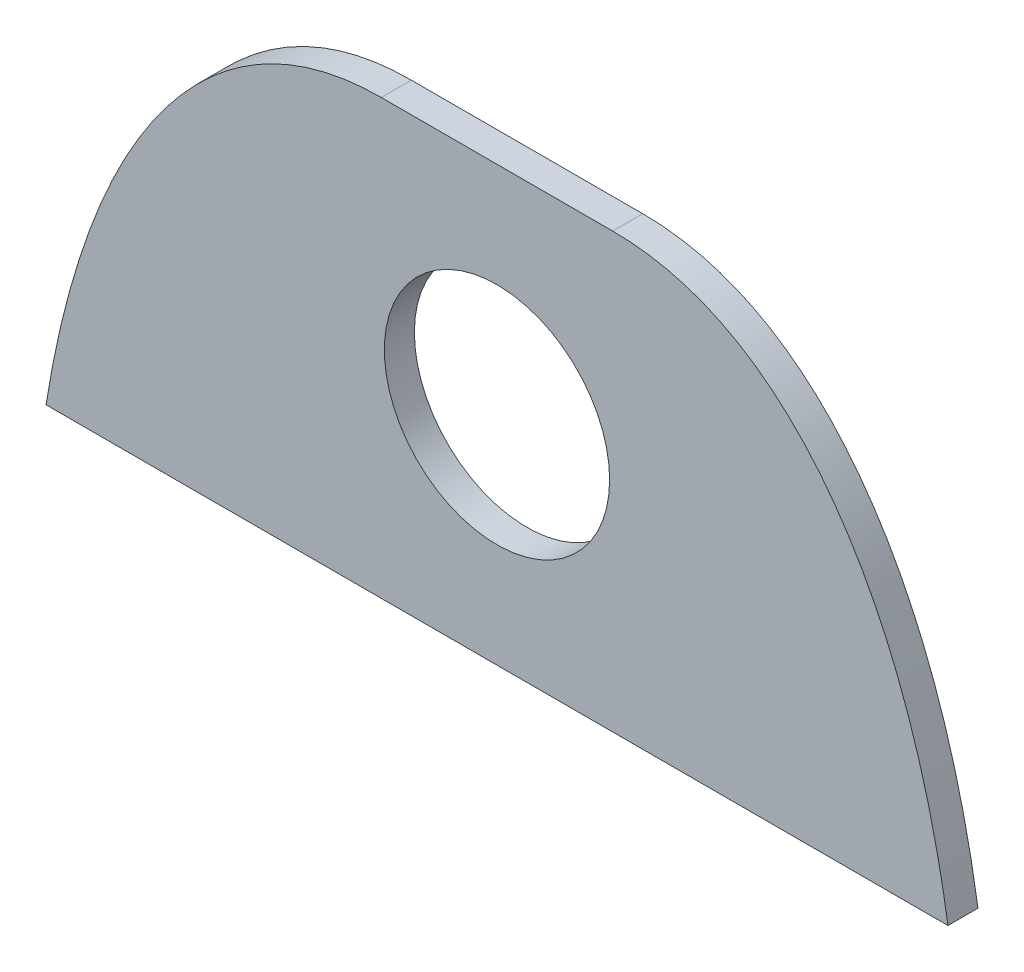
SolidWorks part; units mm, degrees
ref_plane "Front Plane" through (0, 0, 0) normal (0, 0, 1) x (1, 0, 0)
ref_plane "Top Plane" through (0, 0, 0) normal (0, 1, 0) x (1, 0, 0)
ref_plane "Right Plane" through (0, 0, 0) normal (1, 0, 0) x (0, 0, -1)
sketch "Sketch1" plane through (0, 0, 0) normal (0, 0, 1) x (1, 0, 0)
  line L0 (0, 0) -> (15.2522, 0)
  line L1 (9.5827, 7.3353) -> (5.6695, 7.3353)
  spline S0 degree 3 poles (5.6695, 7.3353) (5.244, 7.3353) (4.8287, 7.2747) (4.2224, 7.0847) (4.0246, 7.0051) (3.6475, 6.8192) (3.4665, 6.7125) (3.1184, 6.4738) (2.951, 6.3412) (2.6372, 6.0605) (2.4896, 5.9116) (2.0705, 5.4434) (1.821, 5.0995) (1.1599, 4.0235) (0.8332, 3.2546) (0.4457, 2.055) (0.3347, 1.6477) (0.145, 0.8287) (0.0658, 0.4158) (0, 0) knots 0 0 0 0 0.125 0.125 0.1875 0.1875 0.25 0.25 0.3125 0.3125 0.375 0.375 0.5 0.5 0.75 0.75 0.875 0.875 1 1 1 1
  spline S1 degree 3 poles (15.2522, 0) (15.1207, 0.8307) (14.9375, 1.6469) (14.5531, 2.8407) (14.4065, 3.2335) (14.0654, 4.0056) (13.8724, 4.3812) (13.4322, 5.098) (13.182, 5.443) (12.6226, 6.0682) (12.3136, 6.3497) (11.791, 6.7092) (11.6074, 6.8177) (11.2306, 7.0038) (11.036, 7.0824) (10.6338, 7.2092) (10.4252, 7.2573) (10.0067, 7.3201) (9.7956, 7.3353) (9.5827, 7.3353) knots 0 0 0 0 0.25 0.25 0.375 0.375 0.5 0.5 0.625 0.625 0.75 0.75 0.8125 0.8125 0.875 0.875 0.9375 0.9375 1 1 1 1
extrude "Boss-Extrude1" add sketch "Sketch1" along normal blind 0.508
sketch "Sketch3" plane through (0, 0, 0.508) normal (0, 0, 1) x (1, 0, 0)
  line L0 (7.6261, 0) -> (7.6261, 7.3353) construction
  line L1 (0, 0) -> (15.2522, 0) construction
  line L2 (9.5827, 7.3353) -> (5.6695, 7.3353) construction
  line L3 (7.6261, 3.6677) -> (0, 0) construction
  circle A0 centre (7.6261, 3.6677) radius 1.905
  dimension "D1" = 3.81
extrude "Cut-Extrude1" cut sketch "Sketch3" against normal through all
